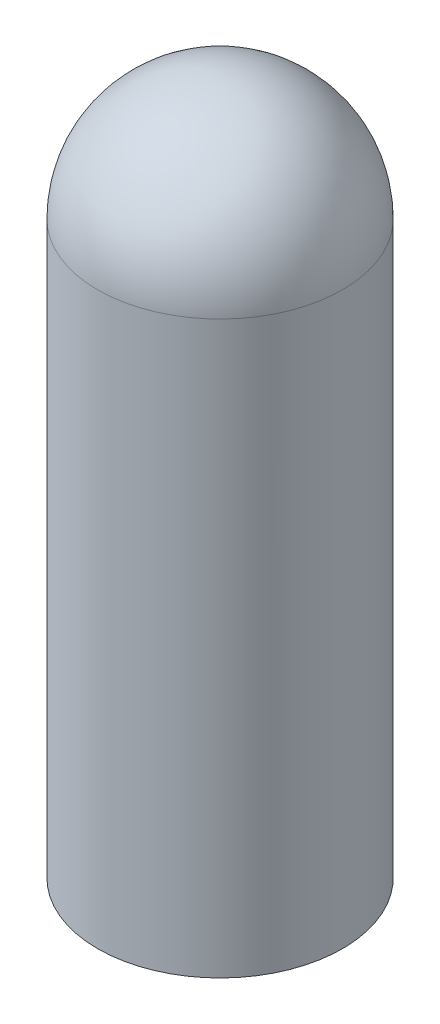
SolidWorks part; units mm, degrees
material "Rubber"
ref_plane "Front Plane" through (0, 0, 0) normal (0, 0, 1) x (1, 0, 0)
ref_plane "Top Plane" through (0, 0, 0) normal (0, 1, 0) x (1, 0, 0)
ref_plane "Right Plane" through (0, 0, 0) normal (1, 0, 0) x (0, 0, -1)
sketch "Sketch1" plane through (0, 0, 0) normal (0, 0, 1) x (1, 0, 0)
  line L0 (-6.731, 0) -> (-6.731, 31.369)
  line L1 (0, 0) -> (0, -6.35) construction
  line L2 (0, -55) -> (0, 55) construction
  line L3 (-6.731, 0) -> (0, 0)
  line L4 (0, 0) -> (0, 38.1)
  arc A0 (-6.731, 31.369) -> (0, 38.1) centre (0, 31.369) cw
  dimension "D1" = 38.1
  dimension "D2" = 13.462
  dimension "D3" = 6.35
  dimension "D4" = 31.369
revolve "Revolve1" add sketch "Sketch1" angle 360 about L1
sketch "Sketch2" plane through (0, 0, 0) normal (0, -1, 0) x (1, 0, 0)
  circle A0 centre (0, 0) radius 6.35
  dimension "D1" = 12.7
extrude "Cut-Extrude1" cut sketch "Sketch2" against normal blind 31.496
